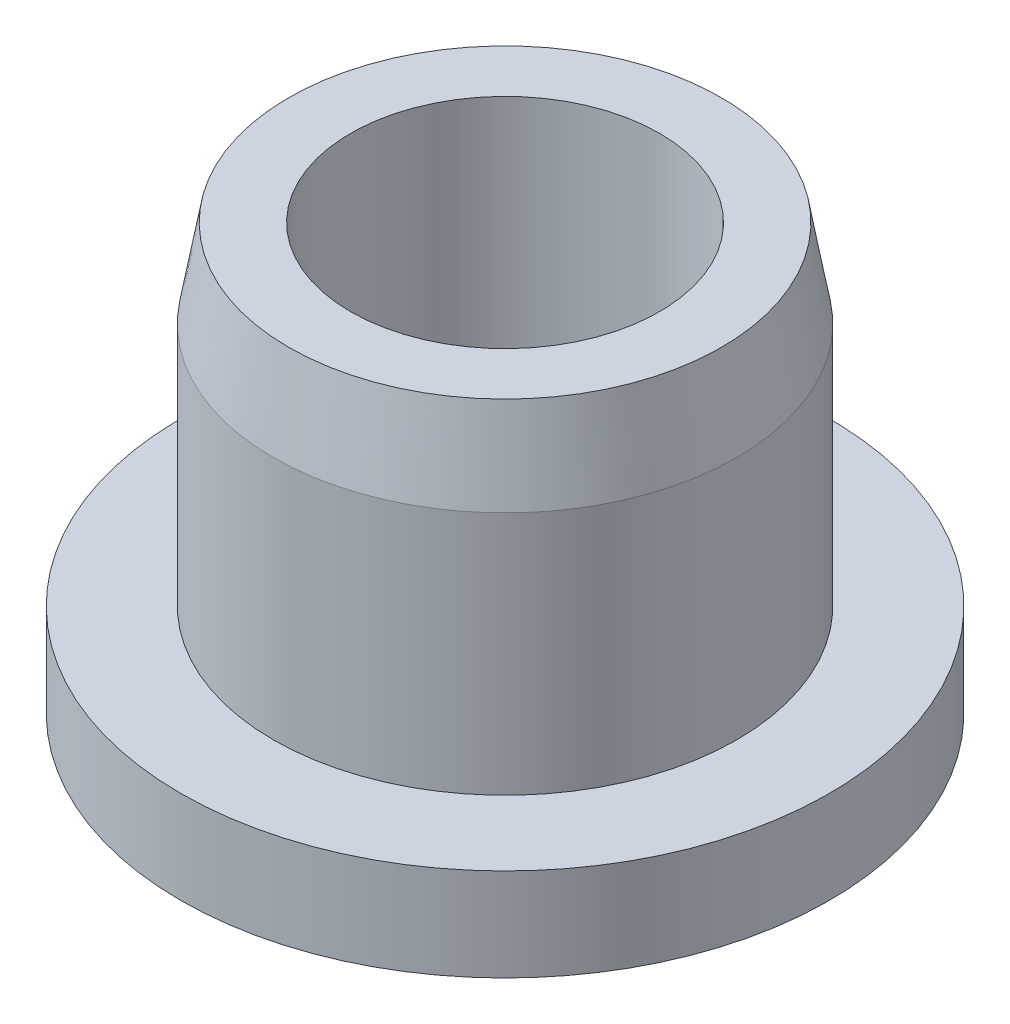
SolidWorks part; units mm, degrees
ref_plane "Front Plane" through (0, 0, 0) normal (0, 0, 1) x (1, 0, 0)
ref_plane "Top Plane" through (0, 0, 0) normal (0, 1, 0) x (1, 0, 0)
ref_plane "Right Plane" through (0, 0, 0) normal (1, 0, 0) x (0, 0, -1)
sketch "Sketch2" plane through (0, 0, 0) normal (0, 1, 0) x (1, 0, 0)
  circle A0 centre (0, 0) radius 4.2
  dimension "D1" = 8.4
extrude "Boss-Extrude1" add sketch "Sketch2" along normal blind 1.2
sketch "Sketch3" plane through (0, 1.2, 0) normal (0, 1, 0) x (1, 0, 0)
  circle A0 centre (0, 0) radius 3
  dimension "D1" = 6
extrude "Boss-Extrude2" add sketch "Sketch3" along normal blind 4.3
sketch "Sketch4" plane through (0, 5.5, 0) normal (0, 1, 0) x (1, 0, 0)
  circle A0 centre (0, 0) radius 2.8
  dimension "D1" = 5.6
extrude "Cut-Extrude1" cut sketch "Sketch4" against normal blind 4.3 draft 10 flip side to cut
sketch "Sketch5" plane through (0, 5.5, 0) normal (0, 1, 0) x (1, 0, 0)
  circle A0 centre (0, 0) radius 2
  dimension "D1" = 4
extrude "Cut-Extrude2" cut sketch "Sketch5" against normal through all
